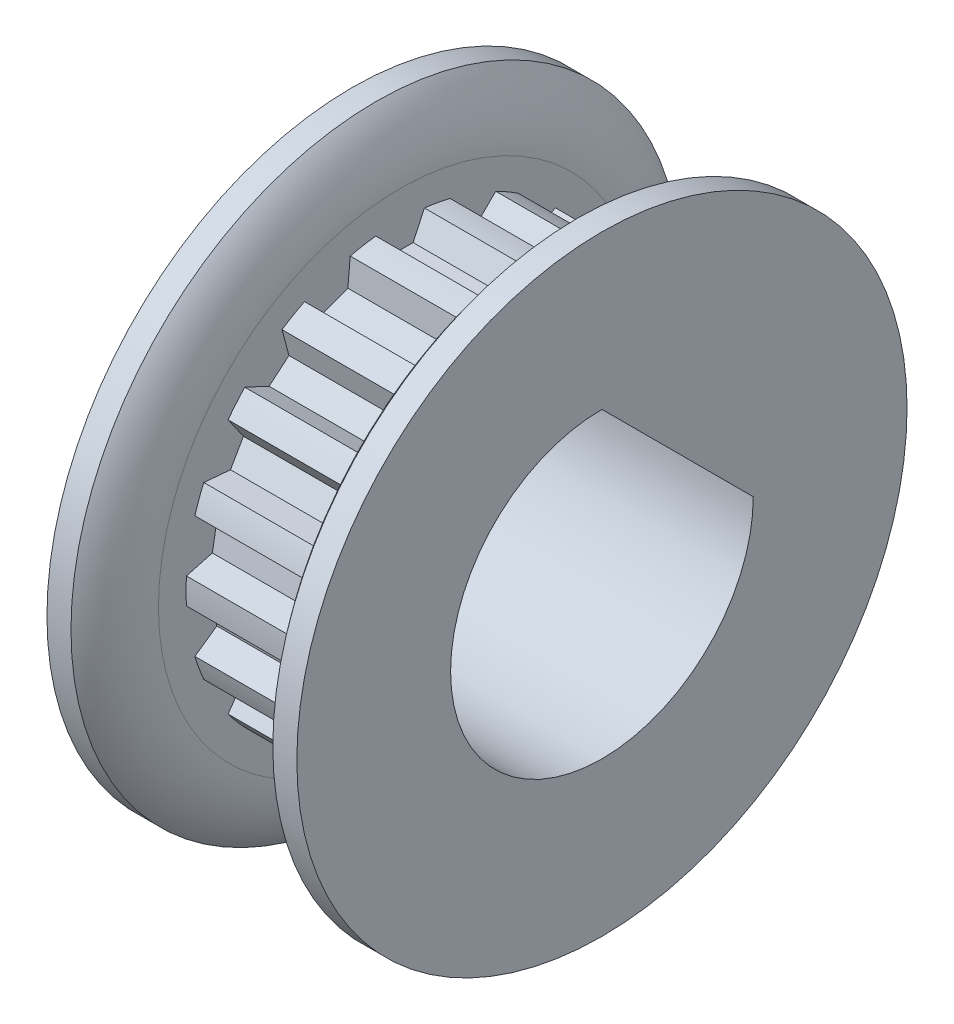
SolidWorks part; units mm, degrees
ref_plane "Front Plane" through (0, 0, 0) normal (0, 0, 1) x (1, 0, 0)
ref_plane "Top Plane" through (0, 0, 0) normal (0, 1, 0) x (1, 0, 0)
ref_plane "Right Plane" through (0, 0, 0) normal (1, 0, 0) x (0, 0, -1)
sketch "Sketch2" plane through (0, 0, 0) normal (1, 0, 0) x (0, 0, -1)
  line L3 (0, 0) -> (0, 4.9911) construction
  line L6 (0, -5.4991) -> (0, -5.8166) construction
  line L7 (-0.5715, 5.4693) -> (-0.343, 4.9793)
  line L8 (0.5715, 5.4693) -> (0.343, 4.9793)
  line L9 (-0.5715, 5.4693) -> (-0.6424, 5.6213)
  line L10 (0.5715, 5.4693) -> (0.6424, 5.6213)
  line L12 (-0.343, 4.9793) -> (0.343, 4.9793)
  line L14 (0, 5.4991) -> (0, 5.8166) construction
  line L15 (0, 0) -> (0, -1.143) construction
  circle A0 centre (0, 0) radius 5.8166 construction
  circle A1 centre (0, 0) radius 4.9911 construction
  circle A2 centre (0, 0) radius 5.4991 construction
  arc A7 (0.6424, 5.6213) -> (-0.6424, 5.6213) centre (0, 0) ccw
  point P5 (0, 5.6578)
  dimension "D3" = 0.3175
  dimension "D1" = 50
sketch "Sketch1" plane through (0, 0, 0) normal (0, 0, 1) x (1, 0, 0)
  line L0 (-6.1468, 0) -> (6.1468, 0) construction
  line L1 (-6.1468, 2.3812) -> (6.1468, 2.3812)
  line L2 (-6.1468, 2.3812) -> (-6.1468, 3.9624)
  line L3 (-0.4572, 8.0645) -> (0.1778, 8.0645)
  line L4 (0.8128, 5.8166) -> (0.8128, 6.3881)
  line L5 (0.8128, 6.9596) -> (0.8128, 5.8166) construction
  line L6 (0.8128, 5.8166) -> (4.8768, 5.8166)
  line L7 (4.8768, 5.8166) -> (4.8768, 6.3881)
  line L8 (4.8768, 5.8166) -> (6.1468, 5.8166) construction
  line L9 (5.5118, 8.0645) -> (6.1468, 8.0645)
  line L10 (6.1468, 8.0645) -> (6.1468, 2.3812)
  line L11 (5.5118, 5.8166) -> (5.5118, 8.0645) construction
  line L12 (-3.302, 3.9624) -> (-3.302, 2.3813) construction
  line L13 (-0.4572, 8.0645) -> (-0.4572, 3.9624)
  line L14 (-0.4572, 3.9624) -> (-6.1468, 3.9624)
  arc A0 (4.8768, 6.3881) -> (5.5118, 8.0645) centre (7.4071, 6.3881) cw
  arc A1 (0.8128, 6.3881) -> (0.1778, 8.0645) centre (-1.7175, 6.3881) ccw
  dimension "Bore Size" = 4.7625
  dimension "Overall Width" = 12.2936
  dimension "Inside Width" = 4.064
  dimension "OD" = 16.129
  dimension "D2" = 11.6332
  dimension "D3" = 1.143
  dimension "D4" = 0.5715
  dimension "Outside Width" = 6.604
revolve "Revolve1" add sketch "Sketch1" angle 360 mid plane about L0
sketch "Sketch4" plane through (0.8128, 0, 0) normal (1, 0, 0) x (0, 0, -1)
  circle A0 centre (0, 0) radius 5.6578
  circle A2 centre (0, 0) radius 5.8166
  circle A3 centre (0, 0) radius 5.8166 construction
extrude "Cut-Extrude2" cut sketch "Sketch4" along normal up to surface (4.064 mm away) up to face at (4.8768, 0, 5.8166)
sketch "Sketch3" plane through (0.8128, 0, 0) normal (1, 0, 0) x (0, 0, -1)
  line L2 (-0.5715, 5.4693) -> (-0.343, 4.9793) construction
  line L3 (-0.343, 4.9793) -> (0.343, 4.9793) construction
  line L4 (0.5715, 5.4693) -> (0.343, 4.9793) construction
  line L5 (-0.6424, 5.6213) -> (-0.343, 4.9793)
  line L6 (-0.343, 4.9793) -> (0.343, 4.9793)
  line L7 (0.6424, 5.6213) -> (0.343, 4.9793)
  arc A1 (0.6424, 5.6213) -> (-0.6424, 5.6213) centre (0, 0) ccw construction
  arc A2 (0.6424, 5.6213) -> (-0.6424, 5.6213) centre (0, 0) ccw
extrude "Cut-Extrude1" cut sketch "Sketch3" along normal up to surface (4.064 mm away) up to face at (4.8768, 0, 6.3881)
pattern_circular "CirPattern1" count 18 over 360 about axis through (0, 0, 0) along (1, 0, 0) of "Cut-Extrude1"
sketch "Sketch5" plane through (0, 0, 0) normal (0, 0, 1) x (1, 0, 0)
  line L1 (4.8768, 6.3881) -> (4.8768, -6.3881) construction
  point P0 (4.8768, 0)
sketch "Sketch6" plane through (0, 0, 0) normal (0, 1, 0) x (1, 0, 0)
  line L0 (-6.1468, 0) -> (-4.7625, 0) construction
  line L1 (-6.1468, 8.0645) -> (-6.1468, -8.0645) construction
  line L2 (-0.4572, 0) -> (-1.8415, 0) construction
  line L4 (-0.4572, 8.0645) -> (-0.4572, -8.0645) construction
  circle A0 centre (-3.302, 0) radius 1.4605
  dimension "D1" = 2.921
extrude "Cut-Extrude3" cut sketch "Sketch6" along normal through all
sketch "Sketch7" plane through (0, 0, 0) normal (0, 0, 1) x (1, 0, 0)
  line L0 (-4.4704, 3.9624) -> (-3.302, 3.9624)
  line L1 (-4.7244, 3.7084) -> (-4.7244, 3.0162)
  line L2 (-4.7244, 3.0162) -> (-4.4704, 2.7622)
  line L3 (-4.4704, 2.7622) -> (-3.302, 2.7622)
  line L4 (-3.302, 2.7622) -> (-3.302, 3.9624) construction
  line L5 (-0.4572, 3.9624) -> (-6.1468, 3.9624) construction
  line L6 (-4.7244, 3.7084) -> (-4.4704, 3.9624)
  line L8 (-3.302, 3.9624) -> (-3.302, 2.7622)
  point P0 (-4.7244, 3.9624)
  point P4 (-4.7244, 2.7622)
  dimension "D1" = 2.8448
  dimension "D2" = 0.381
pattern_circular "CirPattern2" count 2 over 90 about axis through (-6.1468, 0, 0) along (-1, 0, 0) of "Cut-Extrude3"
sketch "Sketch9" plane through (-0.4572, 0, 0) normal (-1, 0, 0) x (0, 0, 1)
  circle A0 centre (0, 0) radius 8.0645
extrude "Cut-Extrude5" cut sketch "Sketch9" along normal up to next
sketch "Sketch10" plane through (6.1468, 0, 0) normal (1, 0, 0) x (0, 0, -1)
  line L0 (0, 4) -> (4, 0)
  circle A0 centre (0, 0) radius 4
  circle A1 centre (0, 0) radius 8.0645
  circle M4 centre (0, 0) radius 2.3812
  dimension "D1" = 8
extrude "Cut-Extrude6" cut sketch "Sketch10" against normal up to next contours L0 A0 M4
equation "\"D3@Sketch2\" = (\"hs@Sketch2\"-\"ht@Sketch2\")/2"
equation "\"D2@Sketch1\" = \"PD@Sketch2\""
equation "\"D3@Sketch1\" = \"hs@Sketch2\""
equation "\"D4@Sketch1\" = \"D3@Sketch1\"/2"
